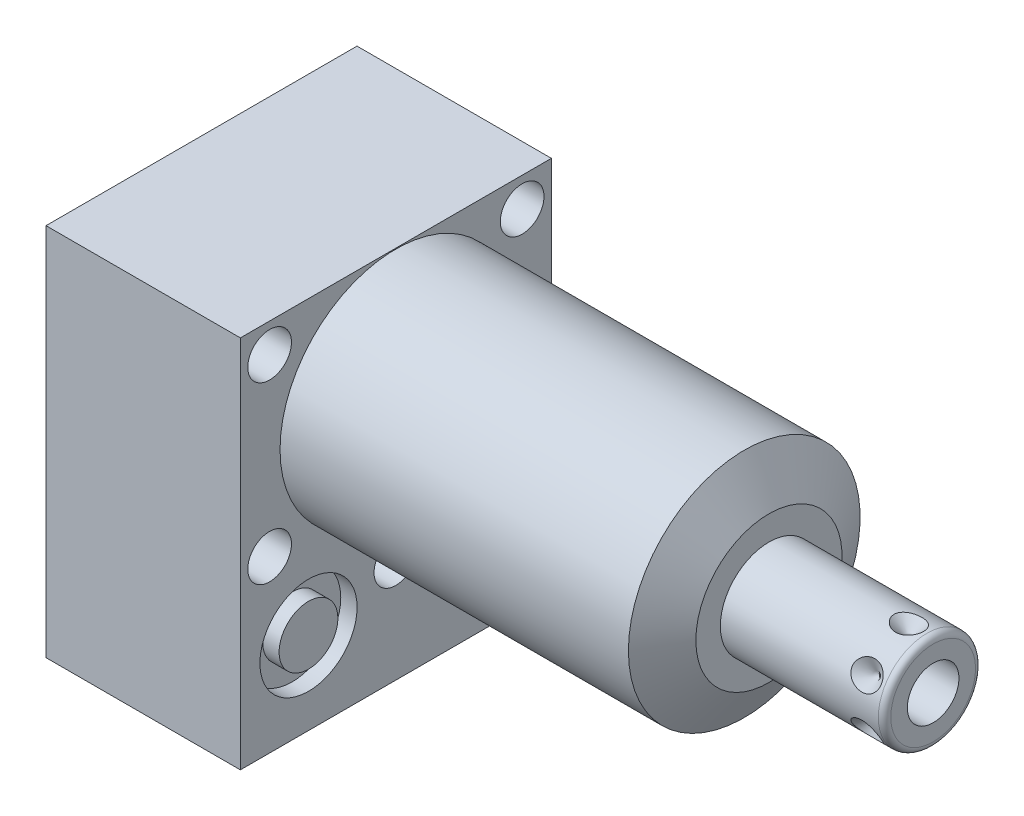
SolidWorks part; units mm, degrees
material "Alloy Steel"
ref_plane "Front Plane" through (0, 0, 0) normal (0, 0, 1) x (1, 0, 0)
ref_plane "Top Plane" through (0, 0, 0) normal (0, 1, 0) x (1, 0, 0)
ref_plane "Right Plane" through (0, 0, 0) normal (1, 0, 0) x (0, 0, -1)
ref_plane "Plane1" through (0, 0, 0) normal (1, 0, 0) x (0, 0, -1)
sketch "Sketch1" plane through (0, 0, 0) normal (1, 0, 0) x (0, 0, -1)
  line L0 (-25.4, 19.05) -> (-25.4, -42.0624)
  line L1 (-25.4, -42.0624) -> (25.4, -42.0624)
  line L2 (25.4, -42.0624) -> (25.4, 19.05)
  line L3 (25.4, 19.05) -> (-25.4, 19.05)
  line L4 (0, -47.0916) -> (0, 22.1996) construction
  dimension "D1" = 50.8
  dimension "D2" = 61.1124
  dimension "D3" = 19.05
extrude "Extrude1" add sketch "Sketch1" along normal blind 60.9346 and the other way blind 31.75
ref_plane "Plane2" through (0, 0, 0) normal (1, 0, 0) x (0, 0, -1)
sketch "Sketch2" plane through (0, 0, 0) normal (1, 0, 0) x (0, 0, -1)
  line L0 (-20.8153, 0) -> (20.8153, 0) construction
  line L6 (25.4, 19.05) -> (-25.4, 19.05)
  line L7 (-25.4, 19.05) -> (-25.4, -42.0624)
  line L8 (-25.4, -42.0624) -> (25.4, -42.0624)
  line L9 (25.4, -42.0624) -> (25.4, 19.05)
  line L10 (25.4, 19.05) -> (-25.4, 19.05)
  line L11 (-25.4, 19.05) -> (-25.4, -42.0624)
  line L12 (-25.4, -42.0624) -> (25.4, -42.0624)
  line L13 (25.4, -42.0624) -> (25.4, 19.05)
  circle A0 centre (0, 0) radius 18.923
  dimension "D1" = 37.846
  dimension "D2" = 0
extrude "Cut-Extrude1" cut sketch "Sketch2" along normal up to next
ref_plane "Plane3" through (0, 0, 0) normal (0, 0, 1) x (1, 0, 0)
sketch "Sketch3" plane through (0, 0, 0) normal (0, 0, 1) x (1, 0, 0)
  line L0 (56.9018, 18.923) -> (60.9346, 11.938)
  line L1 (56.7002, 0) -> (61.1362, 0) construction
  line L2 (60.9346, 18.923) -> (60.9346, 11.938)
  line L3 (60.9346, 18.923) -> (56.9018, 18.923)
  line L4 (60.9346, 18.923) -> (0, 18.923) construction
  line L5 (60.9346, -18.923) -> (60.9346, 18.923) construction
  dimension "D1" = 23.876
  dimension "D2" = 30
revolve "Cut-Revolve1" cut sketch "Sketch3" angle 360 about L1
ref_plane "Plane4" through (-29.083, -28.575, 14.2748) normal (0, 0, 1) x (0, 1, 0)
sketch "S2D0002" plane through (-29.083, -28.575, 14.2748) normal (0, 0, 1) x (0, 1, 0)
  line L0 (0, 0) -> (4.5466, 0)
  line L1 (4.5466, 0) -> (4.1066, -2.0701)
  line L2 (4.1066, -2.0701) -> (3.4544, -2.7223)
  line L3 (3.4544, -2.7223) -> (3.4544, -13.97)
  line L4 (3.4544, -13.97) -> (0, -13.97)
  line L5 (0, -13.97) -> (0, 0)
  line L6 (0, -14.6685) -> (0, 0.6985) construction
  dimension "D1" = 13.97
revolve "Cut-Revolve2" cut sketch "S2D0002" angle 360 about L6
ref_plane "Plane5" through (-29.083, -28.575, -14.2748) normal (0, 0, 1) x (0, 1, 0)
sketch "Sketch5" plane through (-29.083, -28.575, -14.2748) normal (0, 0, 1) x (0, 1, 0)
  line L0 (0, 0) -> (4.5466, 0)
  line L1 (4.5466, 0) -> (4.1066, -2.0701)
  line L2 (4.1066, -2.0701) -> (3.4544, -2.7223)
  line L3 (3.4544, -2.7223) -> (3.4544, -13.97)
  line L4 (3.4544, -13.97) -> (0, -13.97)
  line L5 (0, -13.97) -> (0, 0)
  line L6 (0, -14.6685) -> (0, 0.6985) construction
  dimension "D1" = 13.97
revolve "Cut-Revolve3" cut sketch "Sketch5" angle 360 about L6
ref_plane "Plane6" through (-2.667, -28.575, 14.2748) normal (0, 0, 1) x (0, -1, 0)
sketch "Sketch6" plane through (-2.667, -28.575, 14.2748) normal (0, 0, 1) x (0, -1, 0)
  line L0 (0, 0) -> (4.5466, 0)
  line L1 (4.5466, 0) -> (4.1066, -2.0701)
  line L2 (4.1066, -2.0701) -> (3.4544, -2.7223)
  line L3 (3.4544, -2.7223) -> (3.4544, -12.192)
  line L4 (3.4544, -12.192) -> (0, -12.192)
  line L5 (0, -12.192) -> (0, 0)
  line L6 (0, -12.8016) -> (0, 0.6096) construction
  dimension "D1" = 12.192
revolve "Cut-Revolve4" cut sketch "Sketch6" angle 360 about L6
ref_plane "Plane7" through (-2.667, -28.575, -14.2748) normal (0, 0, 1) x (0, -1, 0)
sketch "Sketch7" plane through (-2.667, -28.575, -14.2748) normal (0, 0, 1) x (0, -1, 0)
  line L0 (0, 0) -> (4.5466, 0)
  line L1 (4.5466, 0) -> (4.1066, -2.0701)
  line L2 (4.1066, -2.0701) -> (3.4544, -2.7223)
  line L3 (3.4544, -2.7223) -> (3.4544, -12.192)
  line L4 (3.4544, -12.192) -> (0, -12.192)
  line L5 (0, -12.192) -> (0, 0)
  line L6 (0, -12.8016) -> (0, 0.6096) construction
  dimension "D1" = 12.192
revolve "Cut-Revolve5" cut sketch "Sketch7" angle 360 about L6
ref_plane "Plane8" through (-15.875, -43.688, 14.2748) normal (0, 0, 1) x (-1, 0, 0)
sketch "Sketch18" plane through (-31.75, 0, 0) normal (-1, 0, 0) x (0, 0, 1)
  circle A0 centre (-14.2748, -28.575) radius 7.9375
  circle A1 centre (14.2748, -28.575) radius 7.9375
  dimension "D1" = 15.875
  dimension "D2" = 15.875
extrude "Cut-Extrude2" cut sketch "Sketch18" against normal blind 2.667
sketch "Sketch19" plane through (0, 0, 0) normal (1, 0, 0) x (0, 0, -1)
  circle A0 centre (-14.2748, -28.575) radius 7.9375
  circle A1 centre (14.2748, -28.575) radius 7.9375
  dimension "D1" = 15.875
  dimension "D2" = 15.875
extrude "Cut-Extrude3" cut sketch "Sketch19" against normal blind 2.667
sketch "Sketch8" plane through (-15.875, -43.688, 14.2748) normal (0, 0, 1) x (-1, 0, 0)
  line L0 (0, -1.8796) -> (6.1849, -1.8796)
  line L1 (6.1849, -1.8796) -> (5.6423, -4.4323)
  line L2 (5.6423, -4.4323) -> (4.9784, -5.0962)
  line L3 (4.9784, -5.0962) -> (4.9784, -20.9296)
  line L4 (4.9784, -20.9296) -> (0, -20.9296)
  line L5 (0, -20.9296) -> (0, -1.8796)
  line L6 (0, -26.67) -> (0, 1.27) construction
  line L7 (15.875, -1.6256) -> (-15.875, -1.6256) construction
  dimension "D1" = 19.05
  dimension "D2" = 0.254
revolve "Cut-Revolve6" cut sketch "Sketch8" angle 360 about L6
ref_plane "Plane9" through (-15.875, -43.688, -14.2748) normal (0, 0, 1) x (-1, 0, 0)
sketch "Sketch9" plane through (-15.875, -43.688, -14.2748) normal (0, 0, 1) x (-1, 0, 0)
  line L0 (0, -1.8796) -> (6.1849, -1.8796)
  line L1 (6.1849, -1.8796) -> (5.6423, -4.4323)
  line L2 (5.6423, -4.4323) -> (4.9784, -5.0962)
  line L3 (4.9784, -5.0962) -> (4.9784, -20.9296)
  line L4 (4.9784, -20.9296) -> (0, -20.9296)
  line L5 (0, -20.9296) -> (0, -1.8796)
  line L6 (0, -26.67) -> (0, 1.27) construction
  line L7 (15.875, -1.6256) -> (-15.875, -1.6256) construction
  dimension "D1" = 19.05
  dimension "D2" = 6.1849
  dimension "D3" = 0.254
revolve "Cut-Revolve7" cut sketch "Sketch9" angle 360 about L6
ref_plane "Plane10" through (0, 0, 0) normal (0, 0, 1) x (1, 0, 0)
sketch "Sketch20" plane through (0, -42.0624, 0) normal (0, -1, 0) x (1, 0, 0)
  circle A0 centre (-15.875, 14.2748) radius 9.525
  circle A1 centre (-15.875, -14.2748) radius 9.525
  dimension "D1" = 19.05
extrude "Cut-Extrude4" cut sketch "Sketch20" against normal blind 0.254
sketch "Sketch10" plane through (0, 0, 0) normal (0, 0, 1) x (1, 0, 0)
  line L0 (60.9346, 0) -> (60.9346, 7.9375)
  line L1 (60.9346, 7.9375) -> (86.741, 7.9375)
  line L2 (87.757, 6.9215) -> (87.757, 0)
  line L3 (87.757, 0) -> (60.9346, 0)
  line L4 (59.5935, 0) -> (89.0981, 0) construction
  line L5 (60.9346, -11.938) -> (60.9346, 11.938) construction
  line L6 (-31.75, 19.05) -> (-31.75, -42.0624) construction
  arc A0 (87.757, 6.9215) -> (86.741, 7.9375) centre (86.741, 6.9215) ccw
  point P0 (60.9346, 0)
  dimension "D2" = 1.016
  dimension "D1" = 15.875
  dimension "D3" = 119.507
revolve "Revolve1" add sketch "Sketch10" angle 360 about L4
ref_plane "Plane11" through (87.757, -4.2164, 0) normal (0, 0, 1) x (0, -1, 0)
sketch "S2D0001" plane through (87.757, -4.2164, 0) normal (0, 0, 1) x (0, -1, 0)
  line L0 (0, 0) -> (0, -15.24)
  line L1 (0, -15.24) -> (-4.2164, -17.7735)
  line L2 (0, 0) -> (-4.2164, 0)
  line L3 (-4.2164, 0) -> (-4.2164, -17.7735)
  line L4 (-4.2164, -24.865) -> (-4.2164, 0.8887) construction
  line L5 (2.7051, 0) -> (-11.1379, 0) construction
  dimension "D1" = 8.4328
  dimension "D2" = 59
  dimension "D3" = 15.24
revolve "Cut-Revolve8" cut sketch "S2D0001" angle 360 about L4
ref_plane "Plane12" through (-31.75, -43.688, 0) normal (0, -1, 0) x (0, 0, -1)
sketch "Sketch12" plane through (-31.75, -41.8084, 0) normal (0, -1, 0) x (0, 0, -1)
  circle A0 centre (-14.2748, 15.875) radius 6.4389
  circle A1 centre (-14.2748, 15.875) radius 9.525 construction
  dimension "D1" = 12.8778
extrude "Extrude2" add sketch "Sketch12" along normal blind 1.651
sketch "Sketch13" plane through (0, 0, 0) normal (1, 0, 0) x (0, 0, -1)
  circle A0 centre (-14.2748, -28.575) radius 4.8006
  circle A1 centre (-14.2748, -28.575) radius 4.5466 construction
  dimension "D1" = 9.6012
ref_plane "Plane13" through (-31.75, 0, 0) normal (1, 0, 0) x (0, 0, -1)
extrude "Extrude3" add sketch "Sketch13" along normal up to surface (2.667 mm away)
ref_plane "Plane14" through (0, -28.575, -14.2748) normal (0, -1, 0) x (0, 0, -1)
sketch "Sketch14" plane through (0, -28.575, -14.2748) normal (0, -1, 0) x (0, 0, -1)
  line L0 (0, -2.8435) -> (0, 1.0401) construction
  line L1 (0, -2.667) -> (0, -4.7371) construction
  line L2 (7.9375, -2.667) -> (-7.9375, -2.667) construction
  circle A0 centre (6.1722, -0.9017) radius 1.7653
  dimension "D1" = 3.5306
  dimension "D2" = 12.3444
revolve "Revolve2" add sketch "Sketch14" angle 360 about L0
ref_plane "Plane15" through (0, -28.575, -14.2748) normal (0, -1, 0) x (0, 0, -1)
sketch "Sketch15" plane through (0, -28.575, -14.2748) normal (0, -1, 0) x (0, 0, -1)
  line L0 (0, -32.7901) -> (0, -28.9065) construction
  line L1 (0, -26.3607) -> (0, -19.4599) construction
  line L2 (-7.9375, -29.083) -> (7.9375, -29.083) construction
  circle A0 centre (6.1722, -30.8483) radius 1.7653
  dimension "D1" = 3.5306
  dimension "D2" = 12.3444
revolve "Revolve3" add sketch "Sketch15" angle 360 about L0
ref_plane "Plane16" through (83.7946, -7.9375, 0) normal (0, 0, 1) x (-1, 0, 0)
sketch "Sketch16" plane through (83.7946, -7.9375, 0) normal (0, 0, 1) x (-1, 0, 0)
  line L0 (0, 0) -> (2.413, 0)
  line L1 (2.413, 0) -> (0, -2.413)
  line L2 (0, 0) -> (0, -2.413)
  line L3 (0, -3.8054) -> (0, 0.1207) construction
  line L4 (22.86, 0) -> (-2.9464, 0) construction
  line L5 (-3.9624, -1.016) -> (-3.9624, -14.859) construction
  dimension "D1" = 3.9624
  dimension "D2" = 4.826
  dimension "D3" = 45
revolve "Cut-Revolve9" cut sketch "Sketch16" angle 360 about L3
pattern_circular "CirPattern1" count 6 over 360 about axis through (60.9356, 0, 0) along (-1, 0, 0) of "Cut-Revolve9"
hole_wizard "Hole1" positions "Sketch22" profile "Sketch21" legacy end condition up to next
sketch "Sketch22" plane through (0, 0, 0) normal (1, 0, 0) x (0, 0, -1)
  line L0 (0, 0) -> (-32.1908, 0) construction
  point P0 (-20.6248, 14.2748)
  point P1 (0, -25.0952)
  point P13 (-20.6248, -14.2748)
  point P14 (20.6248, 14.2748)
  point P15 (20.6248, -14.2748)
  dimension "D2" = 14.2748
  dimension "D3" = 25.0952
sketch "Sketch21" plane through (0, 14.2748, 20.6248) normal (0, 1, 0) x (0, 0, -1)
  line L0 (0, 0) -> (0, 31.75)
  line L1 (0, 31.75) -> (3.5687, 31.75)
  line L2 (3.5687, 31.75) -> (3.5687, 0)
  line L3 (3.5687, 0) -> (0, 0)
  line L4 (0, 110) -> (0, -10) construction
  dimension "Diameter" = 7.1374
  dimension "Depth" = 31.75
sketch "Sketch24" plane through (-29.083, 0, 0) normal (-1, 0, 0) x (0, 0, 1)
  circle A0 centre (14.2748, -28.575) radius 4.8006
  dimension "D1" = 9.6012
extrude "Extrude4" add sketch "Sketch24" along normal blind 2.667
